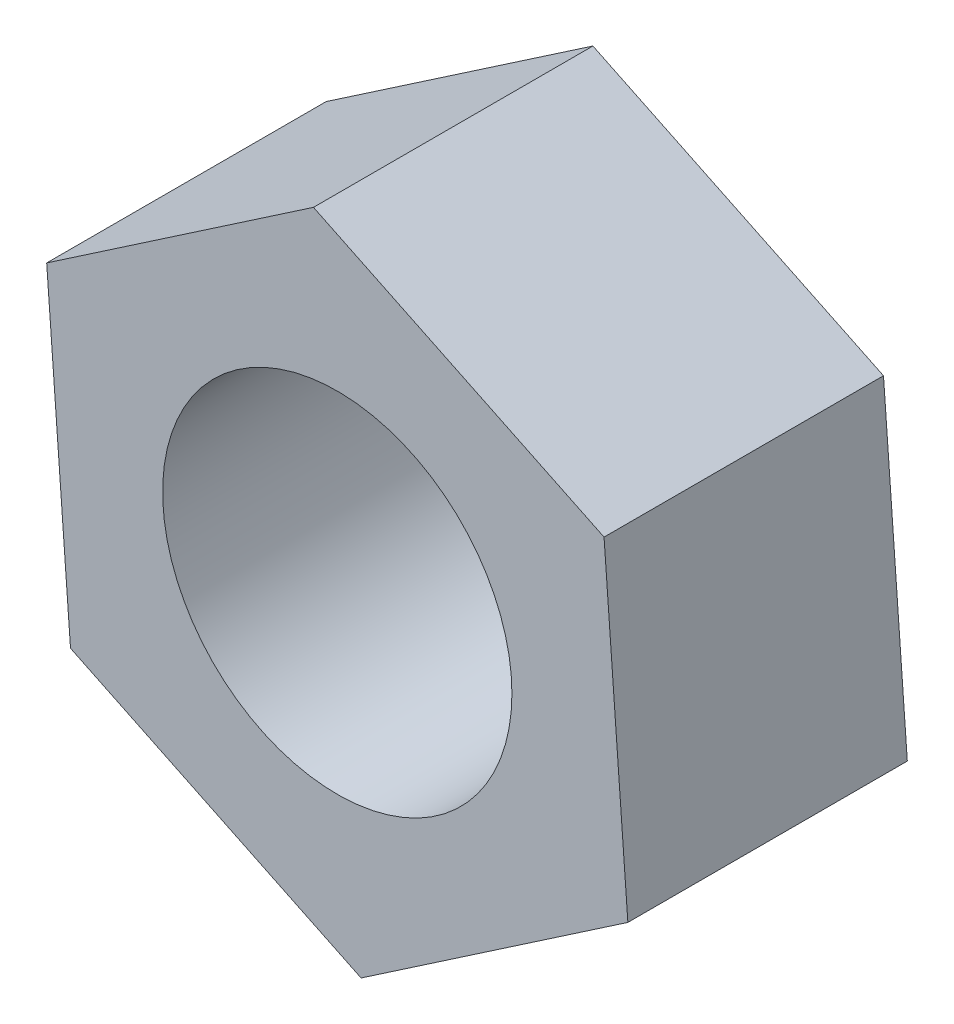
SolidWorks part; units mm, degrees
ref_plane "正面" through (0, 0, 0) normal (0, 0, 1) x (1, 0, 0)
ref_plane "平面" through (0, 0, 0) normal (0, 1, 0) x (1, 0, 0)
ref_plane "右側面" through (0, 0, 0) normal (1, 0, 0) x (0, 0, -1)
sketch "ｽｹｯﾁ1" plane through (0, 0, 0) normal (0, 0, 1) x (1, 0, 0)
  line L1 (-3.8186, -2.5984) -> (0.341, -4.6062)
  line L2 (0.341, -4.6062) -> (4.1596, -2.0078)
  line L3 (4.1596, -2.0078) -> (3.8186, 2.5984)
  line L4 (3.8186, 2.5984) -> (-0.341, 4.6062)
  line L5 (-0.341, 4.6062) -> (-4.1596, 2.0078)
  line L6 (-4.1596, 2.0078) -> (-3.8186, -2.5984)
  circle A0 centre (0, 0) radius 4 construction
  circle A1 centre (0, 0) radius 2.5
  dimension "D2" = 5
  dimension "D1" = 8
extrude "ﾎﾞｽ - 押し出し1" add sketch "ｽｹｯﾁ1" along normal blind 4
